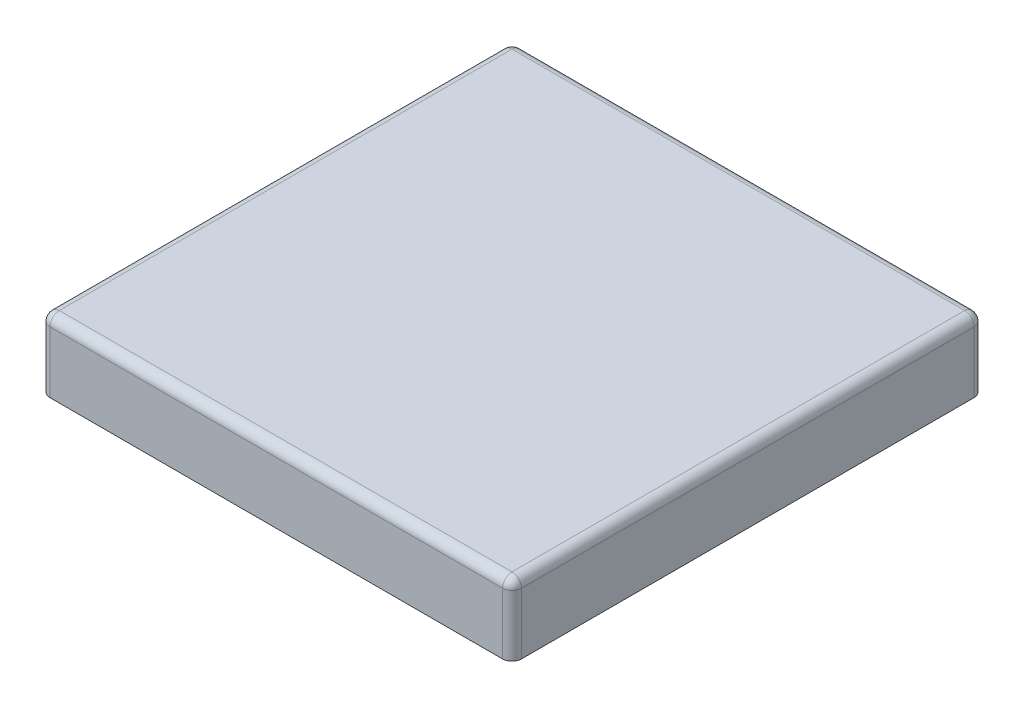
SolidWorks part; units mm, degrees
ref_plane "Front Plane" through (0, 0, 0) normal (0, 0, 1) x (1, 0, 0)
ref_plane "Top Plane" through (0, 0, 0) normal (0, 1, 0) x (1, 0, 0)
ref_plane "Right Plane" through (0, 0, 0) normal (1, 0, 0) x (0, 0, -1)
sketch "Sketch1" plane through (0, 0, 0) normal (0, 1, 0) x (1, 0, 0)
  line L1 (-500, 500) -> (500, 500)
  line L2 (-500, 500) -> (-500, -500)
  line L3 (-500, -500) -> (500, -500)
  line L4 (500, 500) -> (500, -500)
  point P4 (-500, 0)
  point P6 (0, -500)
  dimension "D1" = 1000
  dimension "D2" = 1000
extrude "Boss-Extrude1" add sketch "Sketch1" along normal blind 150
sketch "Sketch2" plane through (0, 0, 0) normal (0, -1, 0) x (1, 0, 0)
  circle A0 centre (0, 0) radius 300
  dimension "D1" = 600
extrude "Cut-Extrude1" cut sketch "Sketch2" against normal blind 100
fillet "Fillet1" radius 20 8 edges at (0, 150, -500) (500, 150, 0) (0, 150, 500) (-500, 150, 0) (500, 75, -500) (500, 75, 500) (-500, 75, 500) (-500, 75, -500)
sketch "Sketch3" plane through (0, 0, 0) normal (0, -1, 0) x (1, 0, 0)
  line L0 (-500, -480) -> (-500, 480) construction
  line L1 (480, -500) -> (-480, -500) construction
  circle A0 centre (-460, -400) radius 10
  dimension "D1" = 20
  dimension "D2" = 40
  dimension "D3" = 100
extrude "Cut-Extrude2" cut sketch "Sketch3" against normal blind 100
mirror "Mirror1" about plane through (0, 0, 0) normal (1, 0, 0) of "Cut-Extrude2"
mirror "Mirror2" about plane through (0, 0, 0) normal (0, 0, 1) of "Mirror1", "Cut-Extrude2"
